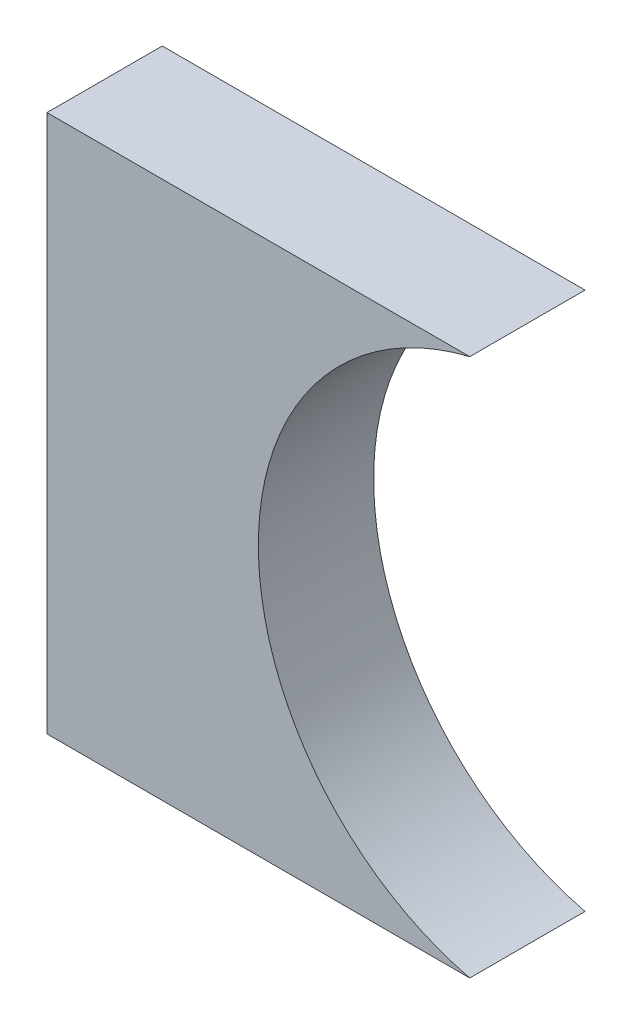
SolidWorks part; units mm, degrees
material "Teak"
ref_plane "Front Plane" through (0, 0, 0) normal (0, 0, 1) x (1, 0, 0)
ref_plane "Top Plane" through (0, 0, 0) normal (0, 1, 0) x (1, 0, 0)
ref_plane "Right Plane" through (0, 0, 0) normal (1, 0, 0) x (0, 0, -1)
sketch "Sketch1" plane through (0, 0, 0) normal (0, 0, 1) x (1, 0, 0)
  line L1 (-34.925, -44.45) -> (34.925, -44.45)
  line L2 (-34.925, -44.45) -> (-34.925, 44.45)
  line L3 (-34.925, 44.45) -> (34.925, 44.45)
  line L4 (34.925, -44.45) -> (34.925, 44.45)
  line L5 (-34.925, -44.45) -> (34.925, 44.45) construction
  line L6 (-34.925, 44.45) -> (34.925, -44.45) construction
  arc A0 (34.925, 44.45) -> (34.925, -44.45) centre (45.7489, 0) ccw
  point P0 (0, 0)
  dimension "D1" = 88.9
  dimension "D2" = 69.85
extrude "Boss-Extrude1" add sketch "Sketch1" along normal mid plane 19.05 contours A0 L3 L2 L1
